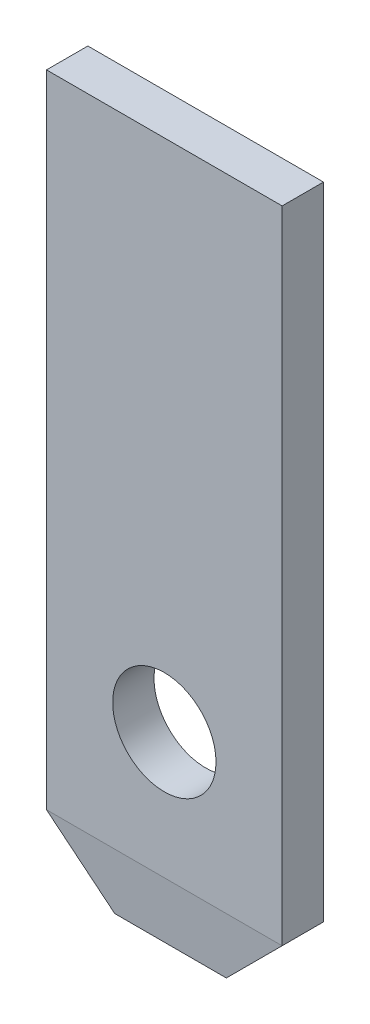
SolidWorks part; units mm, degrees
material "Nickel silver 65-12, UNS C75700"
ref_plane "Front Plane" through (0, 0, 0) normal (0, 0, 1) x (1, 0, 0)
ref_plane "Top Plane" through (0, 0, 0) normal (0, 1, 0) x (1, 0, 0)
ref_plane "Right Plane" through (0, 0, 0) normal (1, 0, 0) x (0, 0, -1)
sketch "Sketch1" plane through (0, 0, 0) normal (0, 0, 1) x (1, 0, 0)
  line L1 (-1.425, 0) -> (1.425, 0)
  line L2 (-1.425, 0) -> (-1.425, 8.5)
  line L3 (-1.425, 8.5) -> (1.425, 8.5)
  line L4 (1.425, 0) -> (1.425, 8.5)
  circle A0 centre (0, 2.275) radius 0.625
  point P0 (-1.425, 0)
  point P3 (1.425, 0)
  dimension "D3" = 1.25
  dimension "D1" = 2.85
  dimension "D2" = 8.5
  dimension "D4" = 2.275
extrude "Extrude1" add sketch "Sketch1" along normal mid plane 0.5
chamfer "Chamfer1" distance 0.075 distance2 0.75 2 edges at (0, 0, -0.25) (0, 0, 0.25)
chamfer "Chamfer2" distance 0.75 angle 45 2 edges at (1.425, 0, 0) (-1.425, 0, 0)
